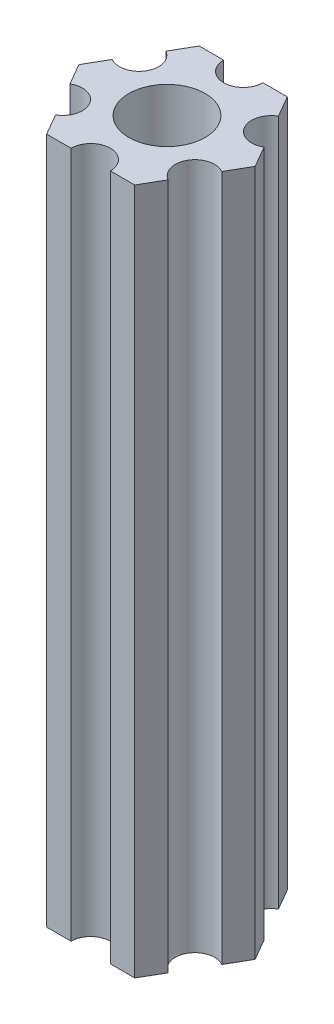
SolidWorks part; units mm, degrees
ref_plane "Front Plane" through (0, 0, 0) normal (0, 0, 1) x (1, 0, 0)
ref_plane "Top Plane" through (0, 0, 0) normal (0, 1, 0) x (1, 0, 0)
ref_plane "Right Plane" through (0, 0, 0) normal (1, 0, 0) x (0, 0, -1)
ref_plane "Plane1" through (0, -57.15, 0) normal (0, -1, 0) x (1, 0, 0)
sketch "Sketch1" plane through (0, -57.15, 0) normal (0, -1, 0) x (1, 0, 0)
  line L0 (-4.6822, -4.5902) -> (-3.6662, -6.35)
  line L1 (-3.6662, -6.35) -> (-1.6342, -6.35)
  line L2 (1.6342, -6.35) -> (3.6662, -6.35)
  line L3 (3.6662, -6.35) -> (4.6822, -4.5902)
  line L4 (6.3163, -1.7598) -> (7.3323, 0)
  line L5 (7.3323, 0) -> (6.3163, 1.7598)
  line L6 (4.6822, 4.5902) -> (3.6662, 6.35)
  line L7 (3.6662, 6.35) -> (1.6342, 6.35)
  line L8 (-1.6342, 6.35) -> (-3.6662, 6.35)
  line L9 (-3.6662, 6.35) -> (-4.6822, 4.5902)
  line L10 (-6.3163, 1.7598) -> (-7.3323, 0)
  line L11 (-7.3323, 0) -> (-6.3163, -1.7598)
  circle A0 centre (0, 0) radius 3.175
  arc A1 (-6.3163, -1.7598) -> (-4.6822, -4.5902) centre (-5.4993, -3.175) cw
  arc A2 (-1.6342, -6.35) -> (1.6342, -6.35) centre (0, -6.35) cw
  arc A3 (4.6822, -4.5902) -> (6.3163, -1.7598) centre (5.4993, -3.175) cw
  arc A4 (6.3163, 1.7598) -> (4.6822, 4.5902) centre (5.4993, 3.175) cw
  arc A5 (1.6342, 6.35) -> (-1.6342, 6.35) centre (0, 6.35) cw
  arc A6 (-4.6822, 4.5902) -> (-6.3163, 1.7598) centre (-5.4993, 3.175) cw
extrude "Boss-Extrude1" add sketch "Sketch1" against normal blind 57.15
